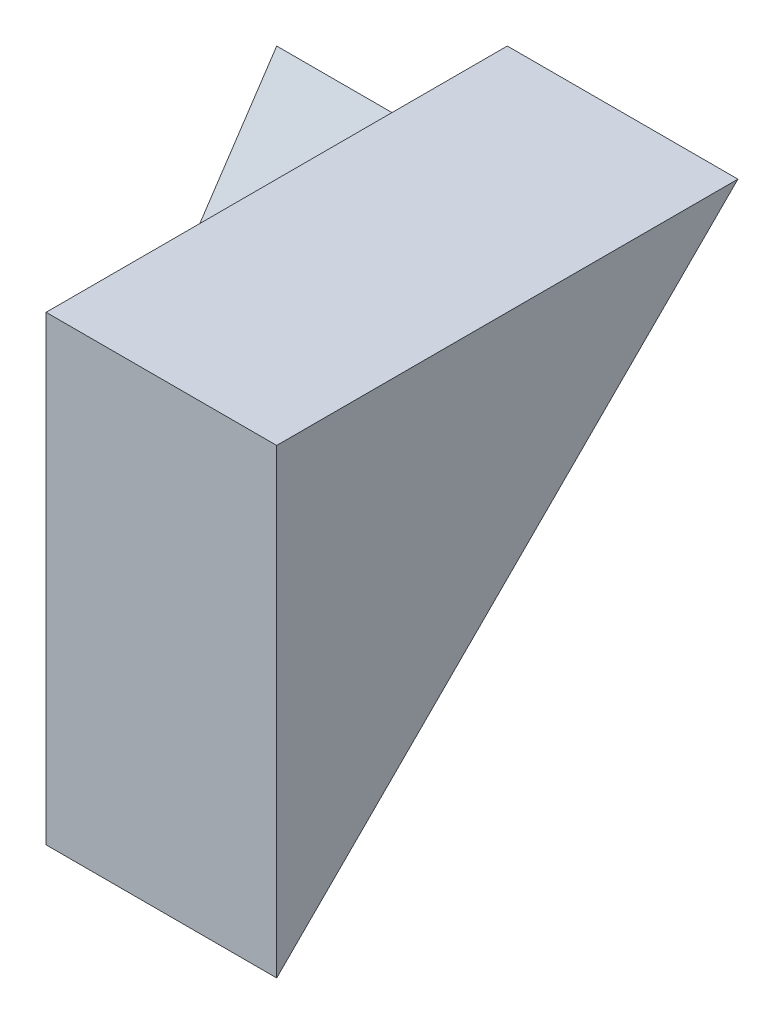
SolidWorks part; units mm, degrees
ref_plane "Front Plane" through (0, 0, 0) normal (0, 0, 1) x (1, 0, 0)
ref_plane "Top Plane" through (0, 0, 0) normal (0, 1, 0) x (1, 0, 0)
ref_plane "Right Plane" through (0, 0, 0) normal (1, 0, 0) x (0, 0, -1)
sketch "Sketch1" plane through (0, 0, 0) normal (1, 0, 0) x (0, 0, -1)
  line L1 (0, 0) -> (4, 0)
  line L2 (0, 0) -> (0, 4)
  line L3 (0, 4) -> (4, 4)
  line L4 (4, 0) -> (4, 4)
  dimension "D1" = 4
  dimension "D2" = 4
extrude "Boss-Extrude1" add sketch "Sketch1" along normal blind 2
sketch "Sketch2" plane through (0, 0, 0) normal (-1, 0, 0) x (0, 0, 1)
  line L1 (-4, 0) -> (-2, 0)
  line L2 (-4, 0) -> (-4, 3)
  line L3 (-4, 3) -> (-2, 3)
  line L4 (-2, 0) -> (-2, 3)
  dimension "D1" = 3
  dimension "D2" = 2
extrude "Boss-Extrude2" add sketch "Sketch2" along normal blind 2
sketch "Sketch3" plane through (-2, 0, 0) normal (-1, 0, 0) x (0, 0, 1)
  line L0 (-4, 3) -> (-2, 3)
  line L1 (-2, 3) -> (-2, 0)
  line L2 (-2, 0) -> (-4, 3)
extrude "Cut-Extrude1" cut sketch "Sketch3" against normal blind 2
sketch "Sketch4" plane through (2, 0, 0) normal (1, 0, 0) x (0, 0, -1)
  line L0 (4, 4) -> (0, 0)
  line L1 (0, 0) -> (0, 4)
  line L2 (0, 4) -> (4, 4)
  line M5 (0, 0) -> (4, 0)
  line M6 (4, 0) -> (4, 4)
extrude "Cut-Extrude2" cut sketch "Sketch4" against normal blind 2 contours L0 M6 M5
